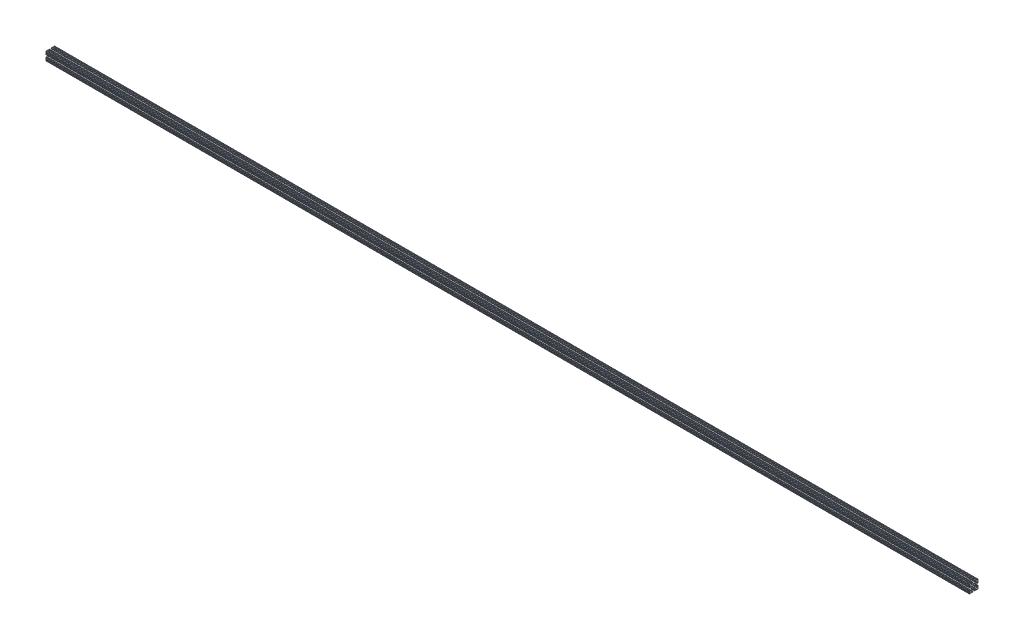
SolidWorks part; units mm, degrees
material "6063-T5"
ref_plane "Front Plane" through (0, 0, 0) normal (0, 0, 1) x (1, 0, 0)
ref_plane "Top Plane" through (0, 0, 0) normal (0, 1, 0) x (1, 0, 0)
ref_plane "Right Plane" through (0, 0, 0) normal (1, 0, 0) x (0, 0, -1)
sketch "Sketch1" plane through (0, 0, 0) normal (1, 0, 0) x (0, 0, -1)
  line L0 (-2.6035, 11.938) -> (-2.6035, 10.922)
  line L1 (-11.938, 12.7) -> (-9.9483, 12.7)
  line L2 (-12.7, 11.938) -> (-12.7, 9.9483)
  line L3 (-11.938, -12.7) -> (-9.9483, -12.7)
  line L4 (12.7, 11.938) -> (12.7, 9.9483)
  line L5 (-12.7, 12.7) -> (12.7, -12.7) construction
  line L6 (-12.7, -12.7) -> (12.7, 12.7) construction
  line L7 (-3.3655, 10.16) -> (-5.7804, 10.16)
  line L8 (-6.3192, 8.8592) -> (-2.8267, 5.3667)
  line L9 (-2.2879, 5.1435) -> (2.2879, 5.1435)
  line L10 (2.8267, 5.3667) -> (6.3192, 8.8592)
  line L11 (5.7804, 10.16) -> (3.3655, 10.16)
  line L12 (2.6035, 10.922) -> (2.6035, 11.938)
  line L13 (-8.6783, 12.7) -> (-6.5617, 12.7)
  line L14 (-5.2917, 12.7) -> (-3.3655, 12.7)
  line L15 (6.5618, 12.7) -> (8.6783, 12.7)
  line L16 (9.9483, 12.7) -> (11.938, 12.7)
  line L17 (3.3655, 12.7) -> (5.2918, 12.7)
  line L18 (10.16, 3.3655) -> (10.16, 5.7804)
  line L19 (8.8592, 6.3192) -> (5.3667, 2.8267)
  line L20 (10.16, -5.7804) -> (10.16, -3.3655)
  line L21 (10.922, -2.6035) -> (11.938, -2.6035)
  line L22 (5.3667, -2.8267) -> (8.8592, -6.3192)
  line L23 (5.1435, 2.2879) -> (5.1435, -2.2879)
  line L24 (11.938, 2.6035) -> (10.922, 2.6035)
  line L25 (3.3655, -10.16) -> (5.7804, -10.16)
  line L26 (6.3192, -8.8592) -> (2.8267, -5.3667)
  line L27 (-5.7804, -10.16) -> (-3.3655, -10.16)
  line L28 (-2.6035, -10.922) -> (-2.6035, -11.938)
  line L29 (-2.8267, -5.3667) -> (-6.3192, -8.8592)
  line L30 (2.2879, -5.1435) -> (-2.2879, -5.1435)
  line L31 (2.6035, -11.938) -> (2.6035, -10.922)
  line L32 (-10.16, -3.3655) -> (-10.16, -5.7804)
  line L33 (-8.8592, -6.3192) -> (-5.3667, -2.8267)
  line L34 (-10.16, 5.7804) -> (-10.16, 3.3655)
  line L35 (-10.922, 2.6035) -> (-11.938, 2.6035)
  line L36 (-5.3667, 2.8267) -> (-8.8592, 6.3192)
  line L37 (-5.1435, -2.2879) -> (-5.1435, 2.2879)
  line L38 (-11.938, -2.6035) -> (-10.922, -2.6035)
  line L39 (-12.7, 8.6783) -> (-12.7, 6.5618)
  line L40 (-12.7, 5.2918) -> (-12.7, 3.3655)
  line L41 (-12.7, -3.3655) -> (-12.7, -5.2917)
  line L42 (-12.7, -6.5617) -> (-12.7, -8.6783)
  line L43 (-12.7, -9.9483) -> (-12.7, -11.938)
  line L44 (-8.6783, -12.7) -> (-6.5618, -12.7)
  line L45 (-5.2918, -12.7) -> (-3.3655, -12.7)
  line L46 (3.3655, -12.7) -> (5.2917, -12.7)
  line L47 (6.5617, -12.7) -> (8.6783, -12.7)
  line L48 (9.9483, -12.7) -> (11.938, -12.7)
  line L49 (12.7, -9.9483) -> (12.7, -11.938)
  line L50 (12.7, -6.5618) -> (12.7, -8.6783)
  line L51 (12.7, -3.3655) -> (12.7, -5.2918)
  line L52 (12.7, 5.2917) -> (12.7, 3.3655)
  line L53 (12.7, 8.6783) -> (12.7, 6.5617)
  arc A1 (5.2918, 12.7) -> (6.5618, 12.7) centre (5.9268, 12.7) ccw
  arc A2 (8.6783, 12.7) -> (9.9483, 12.7) centre (9.3133, 12.7) ccw
  arc A3 (-6.5617, 12.7) -> (-5.2917, 12.7) centre (-5.9267, 12.7) ccw
  arc A4 (-9.9483, 12.7) -> (-8.6783, 12.7) centre (-9.3133, 12.7) ccw
  arc A5 (12.7, 9.9483) -> (12.7, 8.6783) centre (12.7, 9.3133) ccw
  arc A6 (12.7, 6.5617) -> (12.7, 5.2917) centre (12.7, 5.9267) ccw
  arc A7 (12.7, -5.2918) -> (12.7, -6.5618) centre (12.7, -5.9268) ccw
  arc A8 (12.7, -8.6783) -> (12.7, -9.9483) centre (12.7, -9.3133) ccw
  arc A9 (9.9483, -12.7) -> (8.6783, -12.7) centre (9.3133, -12.7) ccw
  arc A10 (6.5617, -12.7) -> (5.2917, -12.7) centre (5.9267, -12.7) ccw
  arc A11 (-5.2918, -12.7) -> (-6.5618, -12.7) centre (-5.9268, -12.7) ccw
  arc A12 (-8.6783, -12.7) -> (-9.9483, -12.7) centre (-9.3133, -12.7) ccw
  arc A13 (-12.7, -9.9483) -> (-12.7, -8.6783) centre (-12.7, -9.3133) ccw
  arc A14 (-12.7, -6.5617) -> (-12.7, -5.2917) centre (-12.7, -5.9267) ccw
  arc A15 (-12.7, 5.2918) -> (-12.7, 6.5618) centre (-12.7, 5.9268) ccw
  arc A16 (-12.7, 8.6783) -> (-12.7, 9.9483) centre (-12.7, 9.3133) ccw
  arc A17 (-11.938, -2.6035) -> (-12.7, -3.3655) centre (-11.938, -3.3655) ccw
  arc A18 (-10.922, -2.6035) -> (-10.16, -3.3655) centre (-10.922, -3.3655) cw
  arc A19 (-10.16, -5.7804) -> (-8.8592, -6.3192) centre (-9.398, -5.7804) ccw
  arc A20 (-6.3192, -8.8592) -> (-5.7804, -10.16) centre (-5.7804, -9.398) ccw
  arc A21 (-3.3655, -10.16) -> (-2.6035, -10.922) centre (-3.3655, -10.922) cw
  arc A22 (-3.3655, -12.7) -> (-2.6035, -11.938) centre (-3.3655, -11.938) ccw
  arc A23 (2.6035, -10.922) -> (3.3655, -10.16) centre (3.3655, -10.922) cw
  arc A24 (2.6035, -11.938) -> (3.3655, -12.7) centre (3.3655, -11.938) ccw
  arc A25 (5.7804, -10.16) -> (6.3192, -8.8592) centre (5.7804, -9.398) ccw
  arc A26 (8.8592, -6.3192) -> (10.16, -5.7804) centre (9.398, -5.7804) ccw
  arc A27 (11.938, -2.6035) -> (12.7, -3.3655) centre (11.938, -3.3655) cw
  arc A28 (10.922, -2.6035) -> (10.16, -3.3655) centre (10.922, -3.3655) ccw
  arc A29 (11.938, 2.6035) -> (12.7, 3.3655) centre (11.938, 3.3655) ccw
  arc A30 (10.922, 2.6035) -> (10.16, 3.3655) centre (10.922, 3.3655) cw
  arc A31 (10.16, 5.7804) -> (8.8592, 6.3192) centre (9.398, 5.7804) ccw
  arc A32 (6.3192, 8.8592) -> (5.7804, 10.16) centre (5.7804, 9.398) ccw
  arc A33 (2.6035, 11.938) -> (3.3655, 12.7) centre (3.3655, 11.938) cw
  arc A34 (3.3655, 10.16) -> (2.6035, 10.922) centre (3.3655, 10.922) cw
  arc A35 (-2.6035, 11.938) -> (-3.3655, 12.7) centre (-3.3655, 11.938) ccw
  arc A36 (-2.6035, 10.922) -> (-3.3655, 10.16) centre (-3.3655, 10.922) cw
  arc A37 (-5.7804, 10.16) -> (-6.3192, 8.8592) centre (-5.7804, 9.398) ccw
  arc A38 (-8.8592, 6.3192) -> (-10.16, 5.7804) centre (-9.398, 5.7804) ccw
  arc A39 (-10.16, 3.3655) -> (-10.922, 2.6035) centre (-10.922, 3.3655) cw
  arc A40 (-11.938, 2.6035) -> (-12.7, 3.3655) centre (-11.938, 3.3655) cw
  arc A41 (11.938, 12.7) -> (12.7, 11.938) centre (11.938, 11.938) cw
  arc A42 (12.7, -11.938) -> (11.938, -12.7) centre (11.938, -11.938) cw
  arc A43 (-11.938, -12.7) -> (-12.7, -11.938) centre (-11.938, -11.938) cw
  arc A44 (-11.938, 12.7) -> (-12.7, 11.938) centre (-11.938, 11.938) ccw
  arc A45 (-2.2879, -5.1435) -> (-2.8267, -5.3667) centre (-2.2879, -5.9055) ccw
  arc A46 (2.2879, -5.1435) -> (2.8267, -5.3667) centre (2.2879, -5.9055) cw
  arc A47 (5.1435, -2.2879) -> (5.3667, -2.8267) centre (5.9055, -2.2879) ccw
  arc A48 (5.3667, 2.8267) -> (5.1435, 2.2879) centre (5.9055, 2.2879) ccw
  arc A49 (-2.8267, 5.3667) -> (-2.2879, 5.1435) centre (-2.2879, 5.9055) ccw
  arc A50 (2.2879, 5.1435) -> (2.8267, 5.3667) centre (2.2879, 5.9055) ccw
  arc A51 (-5.1435, 2.2879) -> (-5.3667, 2.8267) centre (-5.9055, 2.2879) ccw
  arc A52 (-5.1435, -2.2879) -> (-5.3667, -2.8267) centre (-5.9055, -2.2879) cw
  point P0 (0, 0)
  point P17 (0, 5.1435)
  point P92 (0, 0)
  point P124 (2.6035, 12.7)
  point P127 (2.6035, 10.16)
  point P130 (-2.6035, 12.7)
  point P133 (-2.6035, 10.16)
  point P164 (-2.6035, 5.1435)
  point P167 (2.6035, 5.1435)
  dimension "D7" = 1.27
  dimension "D8" = 1.27
  dimension "D9" = 1.27
  dimension "D10" = 1.27
  dimension "D2" = 0.762
  dimension "D16" = 0.762
  dimension "D1" = 25.4
  dimension "D4" = 2.54
  dimension "D5" = 5.207
  dimension "D11" = 3.3867
  dimension "D12" = 3.3866
  dimension "D13" = 3.3867
  dimension "D14" = 3.3867
  dimension "D15" = 4
extrude "Boss-Extrude1" add sketch "Sketch1" along normal blind 2692.4 contours L40 A40 L35 A39 L34 A38 L36 A51 L37 A52 L33 A19 L32 A18 L38 A17 L41 A14 L42 A13 L43 A43 L3 A12 L44 A11 L45 A22 L28 A21 L27 A20 L29 A45 L30 A46 L26 A25 L25 A23 L31 A24 L46 A10 L47 A9 L48 A42 L49 A8 L50 A7 L51 A27 L21 A28 L20 A26 L22 A47 L23 A48 L19 A31 L18 A30 L24 A29 L52 A6 L53 A5 L4 A41 L16 A2 L15 A1 L17 A33 L12 A34 L11 A32 L10 A50 L9 A49 L8 A37 L7 A36 L0 A35 L14 A3 L13 A4 L1 A44 L2 A16 L39 A15
sketch "Sketch2" plane through (0, 0, 0) normal (-1, 0, 0) x (0, 0, 1)
  circle A0 centre (0, 0) radius 2.6035
  dimension "D1" = 5.207
extrude "Cut-Extrude1" cut sketch "Sketch2" against normal up to surface (2692.4 mm away) up to face at (2692.4, 0, 0)
